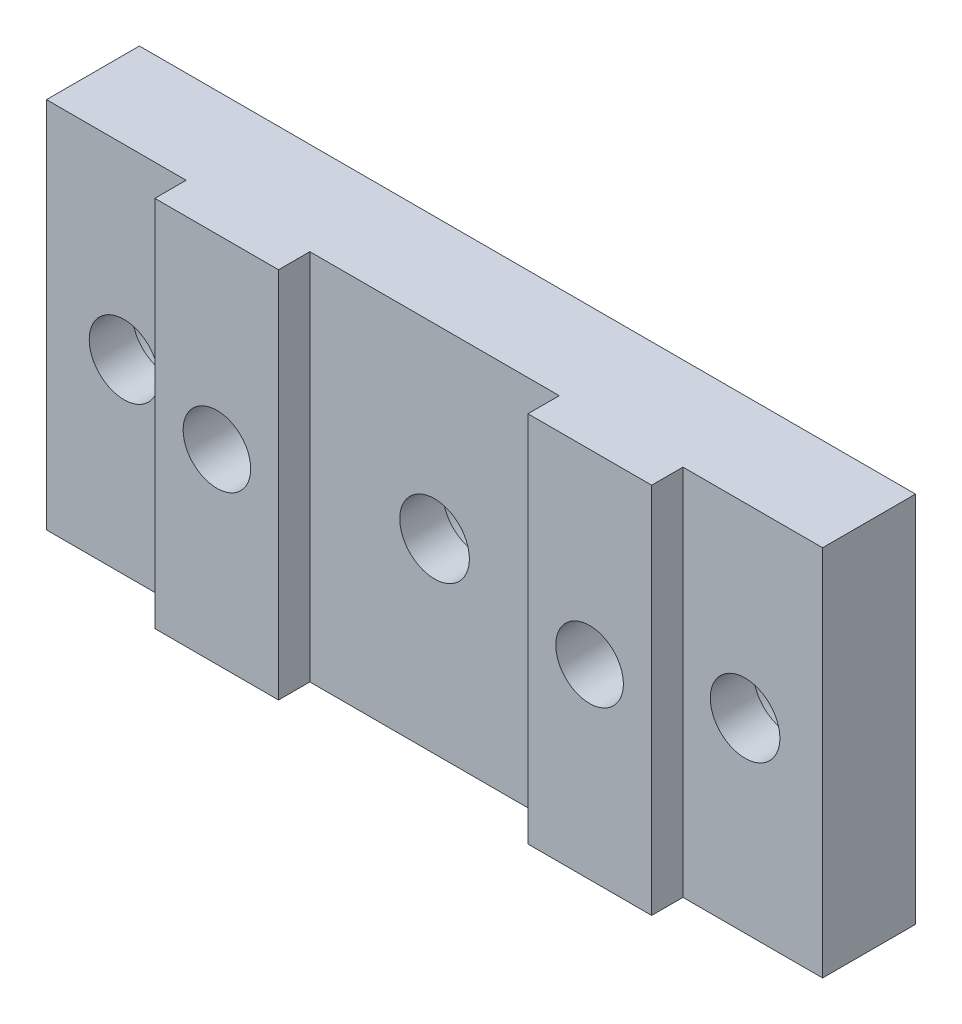
SolidWorks part; units mm, degrees
ref_plane "Front Plane" through (0, 0, 0) normal (0, 0, 1) x (1, 0, 0)
ref_plane "Top Plane" through (0, 0, 0) normal (0, 1, 0) x (1, 0, 0)
ref_plane "Right Plane" through (0, 0, 0) normal (1, 0, 0) x (0, 0, -1)
sketch "Sketch1" plane through (0, 0, 0) normal (0, 0, 1) x (1, 0, 0)
  line L1 (0, 0) -> (39.6748, 0)
  line L2 (0, 0) -> (0, 19.05)
  line L3 (0, 19.05) -> (39.6748, 19.05)
  line L4 (39.6748, 0) -> (39.6748, 19.05)
  dimension "D1" = 19.05
  dimension "D2" = 39.6748
extrude "Extrude1" add sketch "Sketch1" along normal blind 6.35
sketch "Sketch2" plane through (0, 0, 0) normal (0, -1, 0) x (1, 0, 0)
  line L0 (0, 6.35) -> (39.6748, 6.35) construction
  line L1 (0, 6.35) -> (7.1374, 6.35)
  line L2 (0, 6.35) -> (0, 4.7498)
  line L3 (0, 4.7498) -> (7.1374, 4.7498)
  line L4 (7.1374, 6.35) -> (7.1374, 4.7498)
  line L5 (13.462, 6.35) -> (26.2128, 6.35)
  line L6 (13.462, 6.35) -> (13.462, 4.7498)
  line L7 (13.462, 4.7498) -> (26.2128, 4.7498)
  line L8 (26.2128, 6.35) -> (26.2128, 4.7498)
  line L9 (0, 6.35) -> (0, 0) construction
  line L10 (39.6748, 6.35) -> (32.5374, 6.35)
  line L11 (39.6748, 6.35) -> (39.6748, 4.7498)
  line L12 (39.6748, 4.7498) -> (32.5374, 4.7498)
  line L13 (32.5374, 6.35) -> (32.5374, 4.7498)
  dimension "D1" = 1.6002
  dimension "D2" = 7.1374
  dimension "D3" = 13.462
  dimension "D4" = 26.2128
  dimension "D5" = 32.5374
extrude "Cut-Extrude1" cut sketch "Sketch2" against normal through all
hole_wizard "Hole1" positions "Sketch4" profile "Sketch5" legacy end condition through all
sketch "Sketch4" plane through (0, 0, 0) normal (0, 0, -1) x (-1, 0, 0)
  line L0 (0, 0) -> (-39.6748, 0) construction
  line L1 (0, 19.05) -> (0, 0) construction
  point P0 (-3.9624, 9.525)
  point P1 (-19.8374, 9.525)
  point P3 (-35.7124, 9.525)
  dimension "D1" = 9.525
  dimension "D2" = 3.9624
  dimension "D3" = 15.875
  dimension "D4" = 31.75
sketch "Sketch5" plane through (3.9624, 9.525, 0) normal (1, 0, 0) x (0, 1, 0)
  line L0 (0, 0) -> (0, 6.35)
  line L1 (0, 6.35) -> (1.778, 6.35)
  line L2 (1.778, 6.35) -> (1.778, 2.54)
  line L3 (1.778, 2.54) -> (3.175, 2.54)
  line L4 (3.175, 2.54) -> (3.175, 0)
  line L5 (3.175, 0) -> (0, 0)
  line L6 (0, 110) -> (0, -10) construction
  dimension "Diameter" = 3.556
  dimension "Depth" = 6.35
  dimension "C-Bore Diameter" = 6.35
  dimension "C-Bore Depth" = 2.54
hole_wizard "#8-32 Tapped Hole1" positions "Sketch7" profile "Sketch6" tap size "#8-32" standard "Ansi Inch" end condition through all
sketch "Sketch7" plane through (0, 0, 0) normal (0, 0, -1) x (-1, 0, 0)
  line L0 (-39.6748, 19.05) -> (0, 19.05) construction
  line L1 (-39.6748, 0) -> (-39.6748, 19.05) construction
  point P0 (-10.3124, 9.525)
  point P1 (-29.3624, 9.525)
  dimension "D1" = 9.525
  dimension "D2" = 10.3124
  dimension "D3" = 19.05
sketch "Sketch6" plane through (10.3124, 9.525, 0) normal (1, 0, 0) x (0, 1, 0)
  line L0 (0, 0) -> (0, 6.35)
  line L1 (0, 6.35) -> (1.7272, 6.35)
  line L2 (1.7272, 6.35) -> (1.7272, 0)
  line L5 (1.7272, 0) -> (0, 0)
  line L11 (0, -6.35) -> (0, 107.95) construction
  dimension "Thru Tap Drill Dia." = 3.4544
  dimension "Thru Tap Drill Depth" = 6.35
cosmetic thread "Hole Thread1" parameters "D2"=4.1656
cosmetic thread "Hole Thread2" parameters "D2"=4.1656
